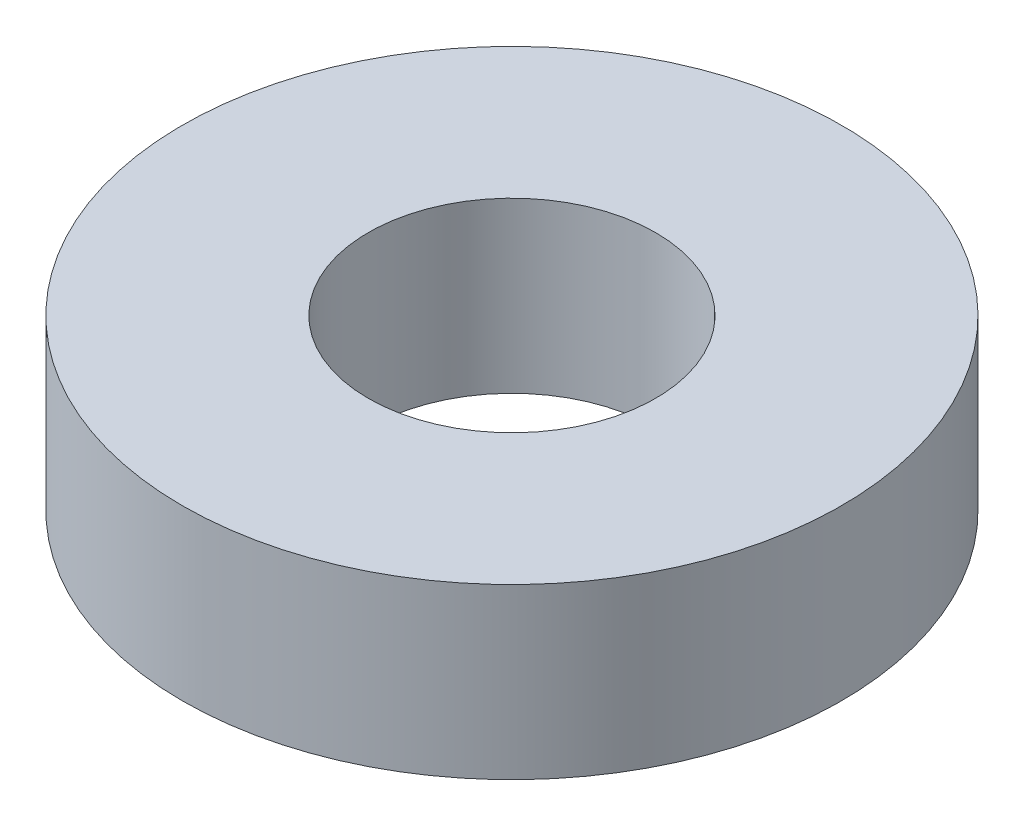
SolidWorks part; units mm, degrees
ref_plane "Front Plane" through (0, 0, 0) normal (0, 0, 1) x (1, 0, 0)
ref_plane "Top Plane" through (0, 0, 0) normal (0, 1, 0) x (1, 0, 0)
ref_plane "Right Plane" through (0, 0, 0) normal (1, 0, 0) x (0, 0, -1)
sketch "Sketch1" plane through (0, 0, 0) normal (0, 1, 0) x (1, 0, 0)
  circle A0 centre (0, 0) radius 3.9
  circle A1 centre (0, 0) radius 1.7
  dimension "D1" = 7.8
  dimension "D2" = 3.4
extrude "Boss-Extrude1" add sketch "Sketch1" along normal blind 2
